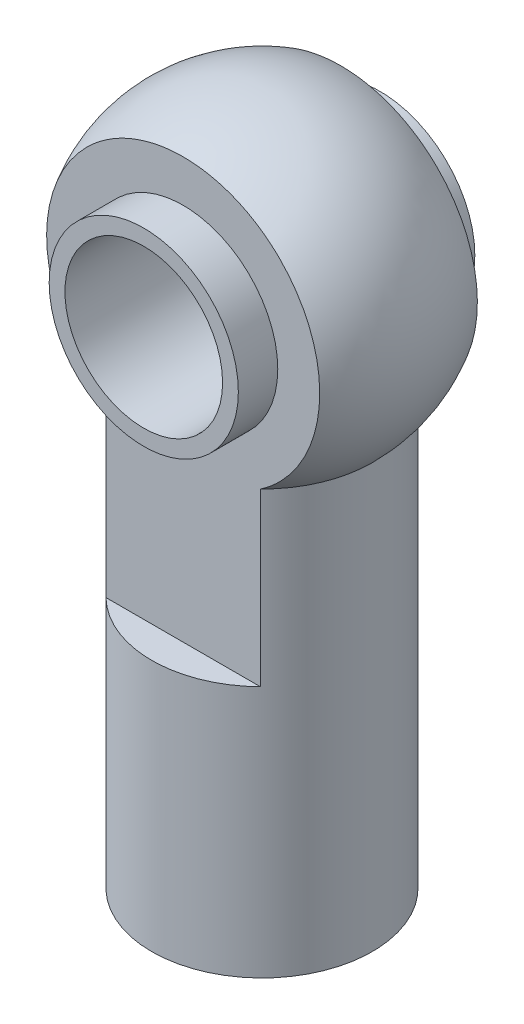
SolidWorks part; units mm, degrees
ref_plane "Front Plane" through (0, 0, 0) normal (0, 0, 1) x (1, 0, 0)
ref_plane "Top Plane" through (0, 0, 0) normal (0, 1, 0) x (1, 0, 0)
ref_plane "Right Plane" through (0, 0, 0) normal (1, 0, 0) x (0, 0, -1)
sketch "Sketch1" plane through (0, 0, 0) normal (0, 0, 1) x (1, 0, 0)
  line L0 (0, 0) -> (0, -7)
  line L1 (1.75, -17) -> (3.5, -17)
  line L2 (3.5, -17) -> (3.5, -3.5707)
  line L3 (0, 0) -> (0, 5)
  line L7 (0, -7) -> (1.75, -7)
  line L8 (1.75, -17) -> (1.75, -7)
  arc A0 (3.5, -3.5707) -> (0, 5) centre (0, 0) ccw
  dimension "D1" = 5
  dimension "D2" = 22
  dimension "D3" = 3.5
  dimension "D4" = 10
  dimension "D5" = 1.75
revolve "Revolve1" add sketch "Sketch1" angle 360 about L3
sketch "Sketch2" plane through (0, 0, 0) normal (0, 0, 1) x (1, 0, 0)
  circle A0 centre (0, 0) radius 2.5
  dimension "D1" = 5
extrude "Cut-Extrude1" cut sketch "Sketch2" against normal through all both and the other way through all
sketch "Sketch3" plane through (0, 0, 0) normal (0, 0, 1) x (1, 0, 0)
  circle A0 centre (0, 0) radius 2.5
ref_plane "Plane1" through (0, 0, 2.5) normal (0, 0, 1) x (1, 0, 0)
sketch "Sketch4" plane through (0, 0, 2.5) normal (0, 0, 1) x (1, 0, 0)
  line L1 (-6, -9) -> (6, -9)
  line L2 (-6, -9) -> (-6, 9)
  line L3 (-6, 9) -> (6, 9)
  line L4 (6, -9) -> (6, 9)
  line L5 (-6, -9) -> (6, 9) construction
  line L6 (-6, 9) -> (6, -9) construction
  point P0 (0, 0)
  dimension "D1" = 18
  dimension "D2" = 12
extrude "Cut-Extrude2" cut sketch "Sketch4" along normal up to next
mirror "Mirror1" about plane through (0, 0, 0) normal (0, 0, 1) of "Cut-Extrude2"
extrude "Extrude-Thin1" add sketch "Sketch3" along normal mid plane 7.5 thin
